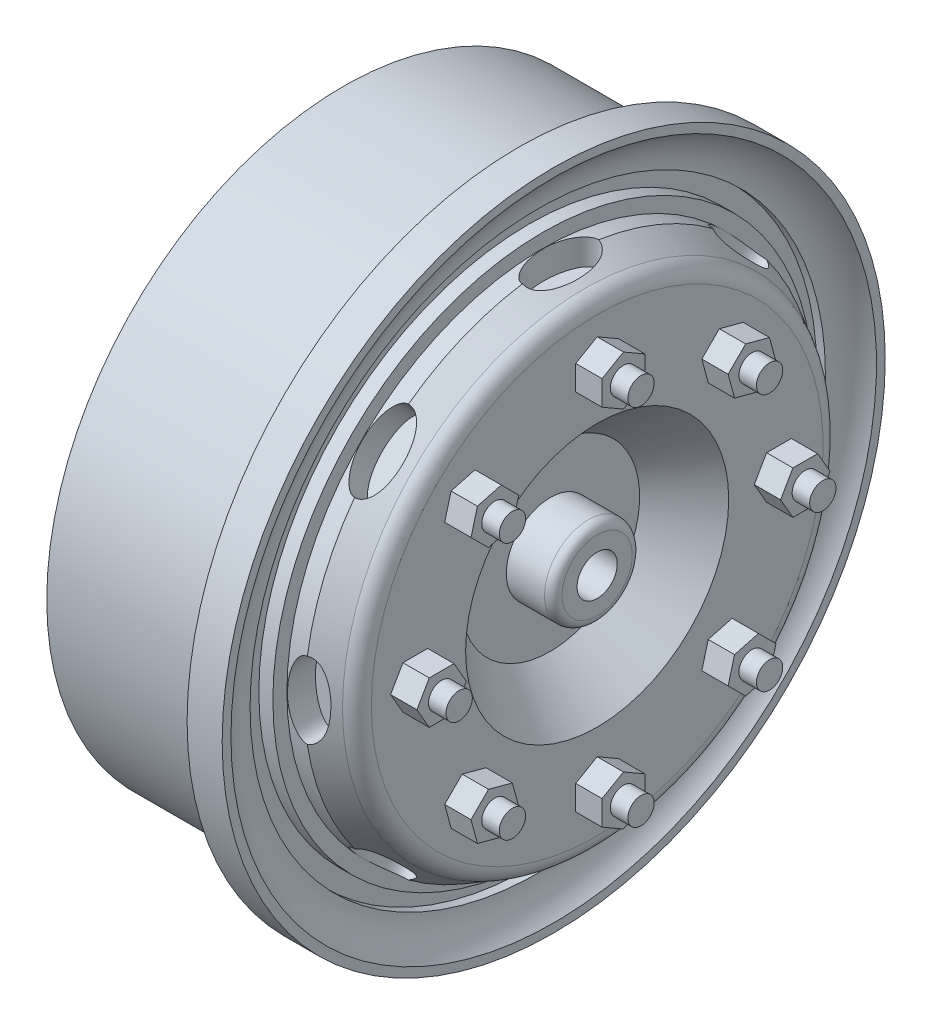
SolidWorks part; units mm, degrees
ref_plane "Front Plane" through (0, 0, 0) normal (0, 0, 1) x (1, 0, 0)
ref_plane "Top Plane" through (0, 0, 0) normal (0, 1, 0) x (1, 0, 0)
ref_plane "Right Plane" through (0, 0, 0) normal (1, 0, 0) x (0, 0, -1)
sketch "Sketch1" plane through (0, 0, 0) normal (0, 1, 0) x (1, 0, 0)
  line L0 (-25, 0) -> (25, 0) construction
  line L1 (0, 20.3358) -> (0, -18.8256) construction
  line L2 (-6, 16.9) -> (4, 16.9)
  line L3 (4, 16.9) -> (4, 18.9)
  line L4 (4, 18.9) -> (6, 18.9)
  line L5 (5.0904, 16.4) -> (4.5904, 16.4)
  line L6 (6, 18.9) -> (6, 18.4)
  line L7 (4.5904, 16.4) -> (4.5904, 15.4)
  line L8 (4.5904, 15.4) -> (5.3904, 15.4)
  line L9 (5.3904, 15.4) -> (5.3904, 14.6)
  line L20 (8.4765, 12.8728) -> (8.4765, 7.5)
  line L25 (5.8, 5.1) -> (8.4765, 7.5)
  line L26 (5.3904, 14.6) -> (6.3904, 14.6)
  line L27 (6.3904, 14.6) -> (7.7848, 13.8241)
  line L28 (-6, 10.5) -> (3.6177, 10.5)
  line L29 (3.6177, 10.5) -> (3.6177, 0)
  line L30 (5.8, 5.1) -> (5.8, 0)
  line L31 (5.8, 0) -> (3.6177, 0)
  line L32 (-6, 16.9) -> (-6, 10.5)
  arc A0 (6, 18.4) -> (5.0904, 16.4) centre (7.7439, 16.4) ccw
  arc A3 (8.4765, 12.8728) -> (7.7848, 13.8241) centre (7.4765, 12.8728) ccw
  point P23 (8.5904, 13.6)
  point P24 (8.4765, 13.6)
  point P25 (8.4765, 13.9348)
  dimension "D17" = 1
  dimension "D15" = 1
  dimension "D1" = 50
  dimension "D2" = 25
  dimension "D3" = 37.8
  dimension "D4" = 2
  dimension "D5" = 2
  dimension "D6" = 10
  dimension "D7" = 6
  dimension "D8" = 0.5
  dimension "D9" = 0.5
  dimension "D10" = 2
  dimension "D11" = 1
  dimension "D12" = 0.8
  dimension "D13" = 0.8
  dimension "D14" = 1
  dimension "D18" = 15
  dimension "D20" = 21
revolve "Revolve1" add sketch "Sketch1" angle 360 about L0
sketch "Sketch2" plane through (5.8, 0, 0) normal (1, 0, 0) x (0, 0, -1)
  circle A0 centre (0, 0) radius 2.5
  dimension "D1" = 5
extrude "Boss-Extrude1" add sketch "Sketch2" along normal up to surface (2.6765 mm away) up to face at (8.4765, 0, 12.8728)
fillet "Fillet2" radius 0.5 1 edges at (8.4765, 0, 2.5)
sketch "Sketch3" plane through (8.4765, 0, 0) normal (1, 0, 0) x (0, 0, -1)
  circle A0 centre (0, 0) radius 1.1449
extrude "Cut-Extrude1" cut sketch "Sketch3" against normal blind 2
ref_plane "Plane1" through (0, 15, 0) normal (0, 1, 0) x (1, 0, 0)
sketch "Sketch4" plane through (0, 15, 0) normal (0, 1, 0) x (1, 0, 0)
  line L0 (-6, 0) -> (7.7848, 0) construction
  line L1 (-6, 16.9) -> (-6, -16.9) construction
  line L2 (7.7848, -13.8241) -> (7.7848, 13.8241) construction
  line L3 (6.3904, -14.6) -> (6.3904, 14.6) construction
  line L4 (8.4765, 0) -> (5.8, 0) construction
  ellipse E0 centre (6.3904, 0) end of major axis (6.3904, -2.1706) minor radius 0.9724
  point P7 (6.3904, 0)
  point P17 (6.3904, -1.8229)
  point P18 (6.3904, -2.1706)
extrude "Cut-Extrude2" cut sketch "Sketch4" against normal blind 2
pattern_circular "CirPattern1" count 8 over 360 about axis through (6.3904, 0, 0) along (-1, 0, 0) of "Cut-Extrude2"
sketch "Sketch5" plane through (8.4765, 0, 0) normal (1, 0, 0) x (0, 0, -1)
  line L0 (6.3326, 6.3326) -> (7.6944, 5.9677)
  line L1 (0, 8.9556) -> (1.2209, 9.6605)
  line L2 (1.2209, 9.6605) -> (1.2209, 11.0703)
  line L3 (1.2209, 11.0703) -> (0, 11.7752)
  line L4 (0, 11.7752) -> (-1.2209, 11.0703)
  line L5 (-1.2209, 11.0703) -> (-1.2209, 9.6605)
  line L6 (-1.2209, 9.6605) -> (0, 8.9556)
  line L7 (7.6944, 5.9677) -> (8.6912, 6.9646)
  line L8 (8.6912, 6.9646) -> (8.3264, 8.3264)
  line L9 (8.3264, 8.3264) -> (6.9646, 8.6912)
  line L10 (6.9646, 8.6912) -> (5.9677, 7.6944)
  line L11 (5.9677, 7.6944) -> (6.3326, 6.3326)
  line L12 (8.9556, 0) -> (9.6605, -1.2209)
  line L13 (9.6605, -1.2209) -> (11.0703, -1.2209)
  line L14 (11.0703, -1.2209) -> (11.7752, 0)
  line L15 (11.7752, 0) -> (11.0703, 1.2209)
  line L16 (11.0703, 1.2209) -> (9.6605, 1.2209)
  line L17 (9.6605, 1.2209) -> (8.9556, 0)
  line L18 (6.3326, -6.3326) -> (5.9677, -7.6944)
  line L19 (5.9677, -7.6944) -> (6.9646, -8.6912)
  line L20 (6.9646, -8.6912) -> (8.3264, -8.3264)
  line L21 (8.3264, -8.3264) -> (8.6912, -6.9646)
  line L22 (8.6912, -6.9646) -> (7.6944, -5.9677)
  line L23 (7.6944, -5.9677) -> (6.3326, -6.3326)
  line L24 (0, -8.9556) -> (-1.2209, -9.6605)
  line L25 (-1.2209, -9.6605) -> (-1.2209, -11.0703)
  line L26 (-1.2209, -11.0703) -> (0, -11.7752)
  line L27 (0, -11.7752) -> (1.2209, -11.0703)
  line L28 (1.2209, -11.0703) -> (1.2209, -9.6605)
  line L29 (1.2209, -9.6605) -> (0, -8.9556)
  line L30 (-6.3326, -6.3326) -> (-7.6944, -5.9677)
  line L31 (-7.6944, -5.9677) -> (-8.6912, -6.9646)
  line L32 (-8.6912, -6.9646) -> (-8.3264, -8.3264)
  line L33 (-8.3264, -8.3264) -> (-6.9646, -8.6912)
  line L34 (-6.9646, -8.6912) -> (-5.9677, -7.6944)
  line L35 (-5.9677, -7.6944) -> (-6.3326, -6.3326)
  line L36 (-8.9556, 0) -> (-9.6605, 1.2209)
  line L37 (-9.6605, 1.2209) -> (-11.0703, 1.2209)
  line L38 (-11.0703, 1.2209) -> (-11.7752, 0)
  line L39 (-11.7752, 0) -> (-11.0703, -1.2209)
  line L40 (-11.0703, -1.2209) -> (-9.6605, -1.2209)
  line L41 (-9.6605, -1.2209) -> (-8.9556, 0)
  line L42 (-6.3326, 6.3326) -> (-5.9677, 7.6944)
  line L43 (-5.9677, 7.6944) -> (-6.9646, 8.6912)
  line L44 (-6.9646, 8.6912) -> (-8.3264, 8.3264)
  line L45 (-8.3264, 8.3264) -> (-8.6912, 6.9646)
  line L46 (-8.6912, 6.9646) -> (-7.6944, 5.9677)
  line L47 (-7.6944, 5.9677) -> (-6.3326, 6.3326)
  circle A0 centre (0, 0) radius 10.3654 construction
  circle A1 centre (0, 10.3654) radius 1.2209 construction
  point P56 (0, 0)
  dimension "D1" = 8
extrude "Boss-Extrude2" add sketch "Sketch5" along normal blind 1.5
sketch "Sketch6" plane through (9.9765, 0, 0) normal (1, 0, 0) x (0, 0, -1)
  line L0 (0, -8.9556) -> (0, -11.7752) construction
  line L1 (-1.2209, -9.6605) -> (1.2209, -11.0703) construction
  circle A0 centre (0, -10.3654) radius 0.75
  circle A1 centre (-7.3295, -7.3295) radius 0.75
  circle A2 centre (-10.3654, 0) radius 0.75
  circle A3 centre (-7.3295, 7.3295) radius 0.75
  circle A4 centre (0, 10.3654) radius 0.75
  circle A5 centre (7.3295, 7.3295) radius 0.75
  circle A6 centre (10.3654, 0) radius 0.75
  circle A7 centre (7.3295, -7.3295) radius 0.75
  point P29 (0, 0)
  dimension "D1" = 1.5
  dimension "D2" = 8
extrude "Boss-Extrude3" add sketch "Sketch6" along normal blind 1
